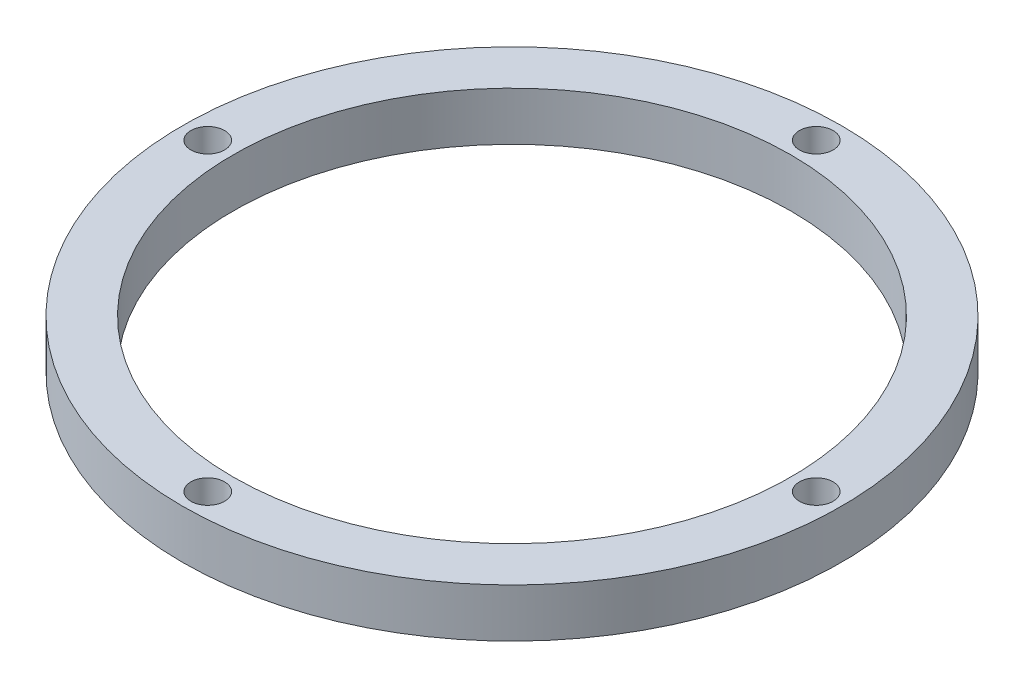
SolidWorks part; units mm, degrees
ref_plane "Front Plane" through (0, 0, 0) normal (0, 0, 1) x (1, 0, 0)
ref_plane "Top Plane" through (0, 0, 0) normal (0, 1, 0) x (1, 0, 0)
ref_plane "Right Plane" through (0, 0, 0) normal (1, 0, 0) x (0, 0, -1)
sketch "Sketch2" plane through (0, 0, 0) normal (0, 1, 0) x (1, 0, 0)
  circle A0 centre (0, 0) radius 32.258
  circle A1 centre (0, 0) radius 27.305
  dimension "D1" = 64.516
  dimension "D2" = 54.61
extrude "Boss-Extrude1" add sketch "Sketch2" along normal blind 4.7625
sketch "Sketch3" plane through (0, 4.7625, 0) normal (0, 1, 0) x (1, 0, 0)
  circle A0 centre (0, 29.7815) radius 1.651
  dimension "D1" = 3.302
  dimension "D2" = 29.7815
extrude "Cut-Extrude1" cut sketch "Sketch3" against normal through all
pattern_circular "CirPattern1" count 4 over 360 about axis through (0, 0, 0) along (0, 1, 0) of "Cut-Extrude1"
